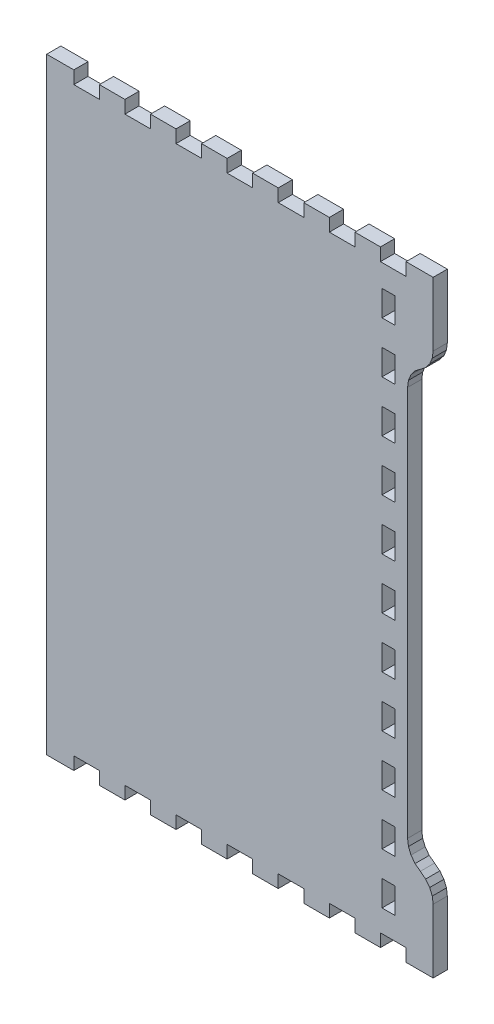
SolidWorks part; units mm, degrees
ref_plane "Front Plane" through (0, 0, 0) normal (0, 0, 1) x (1, 0, 0)
ref_plane "Top Plane" through (0, 0, 0) normal (0, 1, 0) x (1, 0, 0)
ref_plane "Right Plane" through (0, 0, 0) normal (1, 0, 0) x (0, 0, -1)
sketch "Model" plane through (0, 0, 0) normal (0, 0, 1) x (1, 0, 0)
  line L797 (1288.6101, 22.8602) -> (1300.746, 22.8602)
  line L798 (1300.746, 22.8602) -> (1300.746, 28.5752)
  line L799 (1300.746, 28.5752) -> (1312.1767, 28.5752)
  line L800 (1312.1767, 28.5752) -> (1312.1767, 22.8602)
  line L801 (1312.1767, 22.8602) -> (1323.6074, 22.8602)
  line L802 (1323.6074, 22.8602) -> (1323.6074, 28.5752)
  line L803 (1323.6074, 28.5752) -> (1335.0381, 28.5752)
  line L804 (1335.0381, 28.5752) -> (1335.0381, 22.8602)
  line L805 (1335.0381, 22.8602) -> (1346.4653, 22.8602)
  line L806 (1346.4653, 22.8602) -> (1346.4653, 28.5752)
  line L807 (1346.4653, 28.5752) -> (1357.896, 28.5752)
  line L808 (1357.896, 28.5752) -> (1357.896, 22.8602)
  line L809 (1357.896, 22.8602) -> (1369.3268, 22.8602)
  line L810 (1369.3268, 22.8602) -> (1369.3268, 28.5752)
  line L811 (1369.3268, 28.5752) -> (1380.7575, 28.5752)
  line L812 (1380.7575, 28.5752) -> (1380.7575, 22.8602)
  line L813 (1380.7575, 22.8602) -> (1392.1882, 22.8602)
  line L814 (1392.1882, 22.8602) -> (1392.1882, 28.5752)
  line L815 (1392.1882, 28.5752) -> (1403.6154, 28.5752)
  line L816 (1403.6154, 28.5752) -> (1403.6154, 22.8602)
  line L817 (1403.6154, 22.8602) -> (1415.0461, 22.8602)
  line L818 (1415.0461, 22.8602) -> (1415.0461, 28.5752)
  line L819 (1415.0461, 28.5752) -> (1426.4768, 28.5752)
  line L820 (1426.4768, 28.5752) -> (1426.4768, 22.8602)
  line L821 (1426.4768, 22.8602) -> (1437.9075, 22.8602)
  line L822 (1437.9075, 22.8602) -> (1437.9075, 28.5752)
  line L823 (1437.9075, 28.5752) -> (1449.3383, 28.5752)
  line L824 (1449.3383, 28.5752) -> (1449.3383, 22.8602)
  line L825 (1449.3383, 22.8602) -> (1461.4706, 22.8602)
  line L826 (1461.4706, 22.8602) -> (1461.4706, 28.5752)
  line L827 (1461.4706, 28.5752) -> (1461.4706, 51.4354)
  line L828 (1461.4706, 51.4354) -> (1461.0812, 54.3934)
  line L829 (1461.0812, 54.3934) -> (1459.9399, 57.1504)
  line L830 (1459.9399, 57.1504) -> (1458.1239, 59.5176)
  line L831 (1458.1239, 59.5176) -> (1455.7552, 61.3344)
  line L832 (1455.7552, 61.3344) -> (1453.3896, 63.1505)
  line L833 (1453.3896, 63.1505) -> (1451.5741, 65.5172)
  line L834 (1451.5741, 65.5172) -> (1450.4296, 68.2743)
  line L835 (1450.4296, 68.2743) -> (1450.0398, 71.2322)
  line L836 (1450.0398, 71.2322) -> (1450.0398, 245.9182)
  line L837 (1450.0398, 245.9182) -> (1450.4296, 248.8763)
  line L838 (1450.4296, 248.8763) -> (1451.5741, 251.6332)
  line L839 (1451.5741, 251.6332) -> (1453.3896, 254.0001)
  line L840 (1453.3896, 254.0001) -> (1455.7552, 255.8164)
  line L841 (1455.7552, 255.8164) -> (1458.1239, 257.6331)
  line L842 (1458.1239, 257.6331) -> (1459.9399, 260.0004)
  line L843 (1459.9399, 260.0004) -> (1461.0812, 262.7573)
  line L844 (1461.0812, 262.7573) -> (1461.4706, 265.7154)
  line L845 (1461.4706, 265.7154) -> (1461.4706, 288.5754)
  line L846 (1461.4706, 288.5754) -> (1461.4706, 294.2904)
  line L847 (1461.4706, 294.2904) -> (1449.3383, 294.2904)
  line L848 (1449.3383, 294.2904) -> (1449.3383, 288.5754)
  line L849 (1449.3383, 288.5754) -> (1437.9075, 288.5754)
  line L850 (1437.9075, 288.5754) -> (1437.9075, 294.2904)
  line L851 (1437.9075, 294.2904) -> (1426.4768, 294.2904)
  line L852 (1426.4768, 294.2904) -> (1426.4768, 288.5754)
  line L853 (1426.4768, 288.5754) -> (1415.0461, 288.5754)
  line L854 (1415.0461, 288.5754) -> (1415.0461, 294.2904)
  line L855 (1415.0461, 294.2904) -> (1403.6154, 294.2904)
  line L856 (1403.6154, 294.2904) -> (1403.6154, 288.5754)
  line L857 (1403.6154, 288.5754) -> (1392.1882, 288.5754)
  line L858 (1392.1882, 288.5754) -> (1392.1882, 294.2904)
  line L859 (1392.1882, 294.2904) -> (1380.7575, 294.2904)
  line L860 (1380.7575, 294.2904) -> (1380.7575, 288.5754)
  line L861 (1380.7575, 288.5754) -> (1369.3268, 288.5754)
  line L862 (1369.3268, 288.5754) -> (1369.3268, 294.2904)
  line L863 (1369.3268, 294.2904) -> (1357.896, 294.2904)
  line L864 (1357.896, 294.2904) -> (1357.896, 288.5754)
  line L865 (1357.896, 288.5754) -> (1346.4653, 288.5754)
  line L866 (1346.4653, 288.5754) -> (1346.4653, 294.2904)
  line L867 (1346.4653, 294.2904) -> (1335.0381, 294.2904)
  line L868 (1335.0381, 294.2904) -> (1335.0381, 288.5754)
  line L869 (1335.0381, 288.5754) -> (1323.6074, 288.5754)
  line L870 (1323.6074, 288.5754) -> (1323.6074, 294.2904)
  line L871 (1323.6074, 294.2904) -> (1312.1767, 294.2904)
  line L872 (1312.1767, 294.2904) -> (1312.1767, 288.5754)
  line L873 (1312.1767, 288.5754) -> (1300.746, 288.5754)
  line L874 (1300.746, 288.5754) -> (1300.746, 294.2904)
  line L875 (1300.746, 294.2904) -> (1288.6101, 294.2904)
  line L876 (1288.6101, 294.2904) -> (1288.6101, 288.5754)
  line L877 (1288.6101, 288.5754) -> (1288.6101, 28.5752)
  line L878 (1288.6101, 28.5752) -> (1288.6101, 22.8602)
  line L879 (1444.328, 44.2751) -> (1444.328, 38.5601)
  line L880 (1444.328, 38.5601) -> (1438.6127, 38.5601)
  line L881 (1438.6127, 38.5601) -> (1438.6127, 49.9901)
  line L882 (1438.6127, 49.9901) -> (1444.328, 49.9901)
  line L883 (1444.328, 49.9901) -> (1444.328, 44.2751)
  line L884 (1444.328, 67.1351) -> (1444.328, 61.4201)
  line L885 (1444.328, 61.4201) -> (1438.6127, 61.4201)
  line L886 (1438.6127, 61.4201) -> (1438.6127, 72.8501)
  line L887 (1438.6127, 72.8501) -> (1444.328, 72.8501)
  line L888 (1444.328, 72.8501) -> (1444.328, 67.1351)
  line L889 (1444.328, 89.9951) -> (1444.328, 84.2801)
  line L890 (1444.328, 84.2801) -> (1438.6127, 84.2801)
  line L891 (1438.6127, 84.2801) -> (1438.6127, 95.7101)
  line L892 (1438.6127, 95.7101) -> (1444.328, 95.7101)
  line L893 (1444.328, 95.7101) -> (1444.328, 89.9951)
  line L894 (1444.328, 112.8552) -> (1444.328, 107.1402)
  line L895 (1444.328, 107.1402) -> (1438.6127, 107.1402)
  line L896 (1438.6127, 107.1402) -> (1438.6127, 118.5702)
  line L897 (1438.6127, 118.5702) -> (1444.328, 118.5702)
  line L898 (1444.328, 118.5702) -> (1444.328, 112.8552)
  line L899 (1444.328, 135.7152) -> (1444.328, 130.0002)
  line L900 (1444.328, 130.0002) -> (1438.6127, 130.0002)
  line L901 (1438.6127, 130.0002) -> (1438.6127, 141.4302)
  line L902 (1438.6127, 141.4302) -> (1444.328, 141.4302)
  line L903 (1444.328, 141.4302) -> (1444.328, 135.7152)
  line L904 (1444.328, 158.5752) -> (1444.328, 152.8602)
  line L905 (1444.328, 152.8602) -> (1438.6127, 152.8602)
  line L906 (1438.6127, 152.8602) -> (1438.6127, 164.2902)
  line L907 (1438.6127, 164.2902) -> (1444.328, 164.2902)
  line L908 (1444.328, 164.2902) -> (1444.328, 158.5752)
  line L909 (1444.328, 181.4352) -> (1444.328, 175.7202)
  line L910 (1444.328, 175.7202) -> (1438.6127, 175.7202)
  line L911 (1438.6127, 175.7202) -> (1438.6127, 187.1503)
  line L912 (1438.6127, 187.1503) -> (1444.328, 187.1503)
  line L913 (1444.328, 187.1503) -> (1444.328, 181.4352)
  line L914 (1444.328, 204.2953) -> (1444.328, 198.5803)
  line L915 (1444.328, 198.5803) -> (1438.6127, 198.5803)
  line L916 (1438.6127, 198.5803) -> (1438.6127, 210.0103)
  line L917 (1438.6127, 210.0103) -> (1444.328, 210.0103)
  line L918 (1444.328, 210.0103) -> (1444.328, 204.2953)
  line L919 (1444.328, 227.1553) -> (1444.328, 221.4403)
  line L920 (1444.328, 221.4403) -> (1438.6127, 221.4403)
  line L921 (1438.6127, 221.4403) -> (1438.6127, 232.8703)
  line L922 (1438.6127, 232.8703) -> (1444.328, 232.8703)
  line L923 (1444.328, 232.8703) -> (1444.328, 227.1553)
  line L924 (1444.328, 250.0153) -> (1444.328, 244.3003)
  line L925 (1444.328, 244.3003) -> (1438.6127, 244.3003)
  line L926 (1438.6127, 244.3003) -> (1438.6127, 255.7303)
  line L927 (1438.6127, 255.7303) -> (1444.328, 255.7303)
  line L928 (1444.328, 255.7303) -> (1444.328, 250.0153)
  line L929 (1444.328, 272.8754) -> (1444.328, 267.1603)
  line L930 (1444.328, 267.1603) -> (1438.6127, 267.1603)
  line L931 (1438.6127, 267.1603) -> (1438.6127, 278.5904)
  line L932 (1438.6127, 278.5904) -> (1444.328, 278.5904)
  line L933 (1444.328, 278.5904) -> (1444.328, 272.8754)
extrude "Boss-Extrude1" add sketch "Model" along normal blind 6.35
